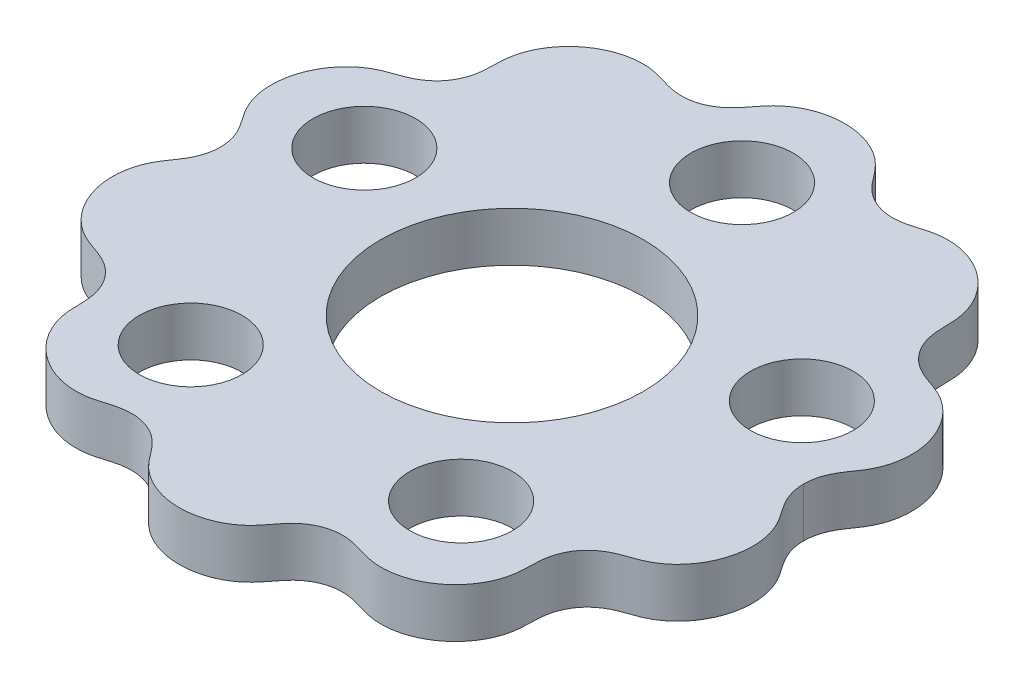
SolidWorks part; units mm, degrees
material "PET"
ref_plane "Front Plane" through (0, 0, 0) normal (0, 0, 1) x (1, 0, 0)
ref_plane "Top Plane" through (0, 0, 0) normal (0, 1, 0) x (1, 0, 0)
ref_plane "Right Plane" through (0, 0, 0) normal (1, 0, 0) x (0, 0, -1)
sketch "Sketch2" plane through (0, 0, 0) normal (0, 1, 0) x (1, 0, 0)
  line L0 (-35.5, 0) -> (35.5, 0) construction
  spline S0 degree 4 poles (33.4858, 18.0026) (33.6819, 17.924) (34.0697, 17.7559) (34.8229, 17.3695) (35.8168, 16.6669) (36.6662, 15.8323) (37.3658, 14.9079) (37.8383, 14.1205) (38.1653, 13.4626) (38.4396, 12.7811) (38.6324, 12.1679) (38.763, 11.6329) (38.856, 11.1412) (38.9196, 10.6952) (38.9638, 10.2049) (38.9806, 9.6712) (38.9658, 9.1373) (38.9248, 8.6719) (38.8693, 8.2752) (38.8096, 7.9474) (38.7602, 7.7184) (38.7131, 7.5241) (38.6709, 7.3649) (38.6347, 7.2368) (38.5942, 7.1034) (38.5498, 6.9652) (38.5069, 6.8376) (38.4719, 6.7392) (38.4232, 6.6091) (38.3681, 6.4683) (38.3132, 6.335) (38.2582, 6.2084) (38.1869, 6.0523) (38.0962, 5.8644) (37.9841, 5.6481) (37.8144, 5.3454) (37.5958, 4.9901) (37.3234, 4.5873) (37.0015, 4.1343) (36.6864, 3.6765) (36.3637, 3.1575) (36.0551, 2.5667) (35.7872, 1.8957) (35.5897, 1.1433) (35.4953, 0.4094) (35.4914, -0.2921) (35.563, -0.9514) (35.6947, -1.5624) (35.9148, -2.2418) (36.2487, -2.9729) (36.7116, -3.7364) (37.2883, -4.5281) (37.8732, -5.3975) (38.3764, -6.3951) (38.8291, -7.7526) (39.0612, -9.4869) (38.9245, -11.2062) (38.4615, -12.8299) (37.8653, -14.1059) (37.2639, -15.0672) (36.5288, -15.9684) (35.6581, -16.7836) (34.7095, -17.4417) (33.7107, -17.9381) (32.726, -18.2865) (31.7989, -18.5913) (30.8389, -19.0081) (29.8914, -19.5994) (29.0166, -20.4069) (28.2897, -21.4373) (27.8234, -22.5309) (27.5826, -23.6177) (27.5037, -24.6512) (27.505, -25.6114) (27.4651, -26.646) (27.3107, -27.5877) (27.0692, -28.4232) (26.6255, -29.5243) (25.9105, -30.7715) (24.7045, -32.1741) (22.8733, -33.4892) (21.0102, -34.2437) (19.2754, -34.5429) (17.8349, -34.5137) (16.7242, -34.3263) (15.7141, -34.0256) (14.7773, -33.7254) (13.7457, -33.4994) (12.6199, -33.4262) (11.4378, -33.5747) (10.2569, -33.9872) (9.2509, -34.5955) (8.4294, -35.3238) (7.7614, -36.1092) (7.196, -36.8901) (6.5586, -37.6989) (5.7796, -38.4701) (4.6502, -39.3075) (3.1026, -40.0593) (1.1762, -40.5363) (-1.0677, -40.5512) (-3.0155, -40.0932) (-4.5978, -39.3403) (-5.7473, -38.4981) (-6.5352, -37.7258) (-7.1782, -36.9144) (-7.7464, -36.1293) (-8.6134, -35.1022) (-9.7345, -34.2099) (-11.1286, -33.6137) (-12.6194, -33.4262) (-13.746, -33.4994) (-14.7771, -33.7254) (-15.7143, -34.0255) (-16.5728, -34.2815) (-17.3671, -34.4346) (-18.2399, -34.5221) (-19.432, -34.5158) (-21.0101, -34.2438) (-22.8733, -33.4892) (-24.7044, -32.1742) (-25.9105, -30.7715) (-26.6256, -29.5243) (-27.0104, -28.5689) (-27.2004, -27.9699) (-27.3615, -27.2769) (-27.4714, -26.489) (-27.5049, -25.6115) (-27.5038, -24.6512) (-27.5826, -23.6178) (-27.8234, -22.5309) (-28.2897, -21.4374) (-29.0166, -20.4069) (-29.8914, -19.5994) (-30.8389, -19.0081) (-31.7989, -18.5913) (-32.726, -18.2865) (-33.7107, -17.9381) (-34.7095, -17.4417) (-35.6581, -16.7836) (-36.5288, -15.9684) (-37.2639, -15.0672) (-37.8653, -14.1059) (-38.4615, -12.8299) (-38.9245, -11.2062) (-39.0612, -9.4869) (-38.8291, -7.7526) (-38.3764, -6.3951) (-37.8732, -5.3975) (-37.2883, -4.5281) (-36.7116, -3.7364) (-36.2487, -2.9729) (-35.9148, -2.2418) (-35.6947, -1.5624) (-35.563, -0.9514) (-35.4914, -0.2921) (-35.4953, 0.4094) (-35.5897, 1.1433) (-35.7872, 1.8957) (-36.0551, 2.5667) (-36.3637, 3.1575) (-36.6864, 3.6765) (-37.0015, 4.1343) (-37.3234, 4.5873) (-37.5958, 4.9901) (-37.8144, 5.3454) (-37.9841, 5.6481) (-38.0962, 5.8644) (-38.1869, 6.0523) (-38.2582, 6.2084) (-38.3132, 6.335) (-38.3681, 6.4683) (-38.4232, 6.6091) (-38.4719, 6.7392) (-38.5069, 6.8376) (-38.5498, 6.9652) (-38.5942, 7.1034) (-38.6347, 7.2368) (-38.6709, 7.3649) (-38.7131, 7.5241) (-38.7602, 7.7184) (-38.8096, 7.9474) (-38.8693, 8.2752) (-38.9248, 8.6719) (-38.9658, 9.1373) (-38.9806, 9.6712) (-38.9638, 10.2049) (-38.9114, 10.7866) (-38.8136, 11.4133) (-38.6599, 12.0804) (-38.4396, 12.7811) (-38.1653, 13.4626) (-37.8383, 14.1205) (-37.3658, 14.9079) (-36.6662, 15.8323) (-35.8168, 16.6669) (-34.8229, 17.3695) (-34.0697, 17.7559) (-33.6819, 17.924) (-33.4858, 18.0026) knots 0 0 0 0 0 0.004809 0.009619 0.019238 0.027591 0.031768 0.035945 0.040122 0.044299 0.048476 0.050565 0.052653 0.055691 0.058728 0.061766 0.064804 0.067841 0.06936 0.070879 0.072398 0.073157 0.073916 0.074676 0.075435 0.076195 0.076954 0.077745 0.078536 0.079326 0.080117 0.080908 0.081698 0.08328 0.084861 0.086443 0.089606 0.092769 0.095932 0.099095 0.102258 0.106673 0.111089 0.115505 0.11992 0.123472 0.127023 0.130575 0.134126 0.139703 0.145279 0.150856 0.156432 0.163531 0.17063 0.183308 0.195985 0.202422 0.20886 0.215297 0.221734 0.22883 0.235926 0.241481 0.247037 0.252592 0.258148 0.265247 0.272347 0.279497 0.286646 0.292113 0.297579 0.303046 0.308512 0.315658 0.31923 0.322803 0.335512 0.348221 0.360938 0.373655 0.380833 0.388011 0.39361 0.39921 0.404809 0.410408 0.417591 0.424773 0.431727 0.438681 0.44417 0.44966 0.455149 0.460639 0.467587 0.474534 0.487038 0.499543 0.512347 0.52515 0.532151 0.539153 0.544668 0.550183 0.555698 0.561213 0.575227 0.582409 0.589592 0.595191 0.60079 0.60639 0.611989 0.615578 0.619167 0.626345 0.639062 0.651779 0.664488 0.677197 0.68077 0.684342 0.687915 0.691488 0.696954 0.702421 0.707887 0.713354 0.720503 0.727653 0.734753 0.741852 0.747408 0.752963 0.758519 0.764074 0.77117 0.778266 0.784703 0.79114 0.797578 0.804015 0.816692 0.82937 0.836469 0.843568 0.849144 0.854721 0.860297 0.865874 0.869425 0.872977 0.876528 0.88008 0.884495 0.888911 0.893327 0.897742 0.900905 0.904068 0.907231 0.910394 0.913557 0.915139 0.91672 0.918302 0.919092 0.919883 0.920674 0.921464 0.922255 0.923046 0.923805 0.924565 0.925324 0.926084 0.926843 0.927602 0.929121 0.93064 0.932159 0.935196 0.938234 0.941272 0.944309 0.947347 0.951524 0.955701 0.959878 0.964055 0.968232 0.972409 0.980762 0.990381 0.995191 1 1 1 1 1 construction
  spline S1 degree 4 poles (35.5, 0) (35.5, -0.0043) (35.5002, -0.1647) (35.5119, -0.481) (35.563, -0.9514) (35.6947, -1.5624) (35.9148, -2.2418) (36.2487, -2.9729) (36.7116, -3.7364) (37.2883, -4.5281) (37.8732, -5.3975) (38.3764, -6.3951) (38.8291, -7.7526) (39.0612, -9.4869) (38.9245, -11.2062) (38.4615, -12.8299) (37.8653, -14.1059) (37.2639, -15.0672) (36.5288, -15.9684) (35.6581, -16.7836) (34.7095, -17.4417) (33.7107, -17.9381) (32.726, -18.2865) (31.7989, -18.5913) (30.8389, -19.0081) (29.8914, -19.5994) (29.0166, -20.4069) (28.2897, -21.4373) (27.8234, -22.5309) (27.5826, -23.6177) (27.5037, -24.6512) (27.505, -25.6114) (27.4651, -26.646) (27.3107, -27.5877) (27.0692, -28.4232) (26.6255, -29.5243) (25.9105, -30.7715) (24.7045, -32.1741) (22.8733, -33.4892) (21.0102, -34.2437) (19.2754, -34.5429) (17.8349, -34.5137) (16.7242, -34.3263) (15.7141, -34.0256) (14.7773, -33.7254) (13.7457, -33.4994) (12.6199, -33.4262) (11.4378, -33.5747) (10.2569, -33.9872) (9.2509, -34.5955) (8.4294, -35.3238) (7.7614, -36.1092) (7.196, -36.8901) (6.5586, -37.6989) (5.7796, -38.4701) (4.6502, -39.3075) (3.1026, -40.0593) (1.1762, -40.5363) (-1.0677, -40.5512) (-3.0155, -40.0932) (-4.5978, -39.3403) (-5.7473, -38.4981) (-6.5352, -37.7258) (-7.1782, -36.9144) (-7.7464, -36.1293) (-8.6134, -35.1022) (-9.7345, -34.2099) (-11.1286, -33.6137) (-12.6194, -33.4262) (-13.746, -33.4994) (-14.7771, -33.7254) (-15.7143, -34.0255) (-16.5728, -34.2815) (-17.3671, -34.4346) (-18.2399, -34.5221) (-19.432, -34.5158) (-21.0101, -34.2438) (-22.8733, -33.4892) (-24.7044, -32.1742) (-25.9105, -30.7715) (-26.6256, -29.5243) (-27.0104, -28.5689) (-27.2004, -27.9699) (-27.3615, -27.2769) (-27.4714, -26.489) (-27.5049, -25.6115) (-27.5038, -24.6512) (-27.5826, -23.6178) (-27.8234, -22.5309) (-28.2897, -21.4374) (-29.0166, -20.4069) (-29.8914, -19.5994) (-30.8389, -19.0081) (-31.7989, -18.5913) (-32.726, -18.2865) (-33.7107, -17.9381) (-34.7095, -17.4417) (-35.6581, -16.7836) (-36.5288, -15.9684) (-37.2639, -15.0672) (-37.8653, -14.1059) (-38.4615, -12.8299) (-38.9245, -11.2062) (-39.0612, -9.4869) (-38.8291, -7.7526) (-38.3764, -6.3951) (-37.8732, -5.3975) (-37.2883, -4.5281) (-36.7116, -3.7364) (-36.2487, -2.9729) (-35.9148, -2.2418) (-35.6947, -1.5624) (-35.563, -0.9514) (-35.5119, -0.481) (-35.5002, -0.1647) (-35.5, -0.0043) (-35.5, 0) knots 0.119822 0.119822 0.119822 0.119822 0.119822 0.11992 0.123472 0.127023 0.130575 0.134126 0.139703 0.145279 0.150856 0.156432 0.163531 0.17063 0.183308 0.195985 0.202422 0.20886 0.215297 0.221734 0.22883 0.235926 0.241481 0.247037 0.252592 0.258148 0.265247 0.272347 0.279497 0.286646 0.292113 0.297579 0.303046 0.308512 0.315658 0.31923 0.322803 0.335512 0.348221 0.360938 0.373655 0.380833 0.388011 0.39361 0.39921 0.404809 0.410408 0.417591 0.424773 0.431727 0.438681 0.44417 0.44966 0.455149 0.460639 0.467587 0.474534 0.487038 0.499543 0.512347 0.52515 0.532151 0.539153 0.544668 0.550183 0.555698 0.561213 0.575227 0.582409 0.589592 0.595191 0.60079 0.60639 0.611989 0.615578 0.619167 0.626345 0.639062 0.651779 0.664488 0.677197 0.68077 0.684342 0.687915 0.691488 0.696954 0.702421 0.707887 0.713354 0.720503 0.727653 0.734753 0.741852 0.747408 0.752963 0.758519 0.764074 0.77117 0.778266 0.784703 0.79114 0.797578 0.804015 0.816692 0.82937 0.836469 0.843568 0.849144 0.854721 0.860297 0.865874 0.869425 0.872977 0.876528 0.88008 0.880178 0.880178 0.880178 0.880178 0.880178
  spline S2 degree 4 poles (35.5, 0) (35.5, 0.0043) (35.5002, 0.1647) (35.5119, 0.481) (35.563, 0.9514) (35.6947, 1.5624) (35.9148, 2.2418) (36.2487, 2.9729) (36.7116, 3.7364) (37.2883, 4.5281) (37.8732, 5.3975) (38.3764, 6.3951) (38.8291, 7.7526) (39.0612, 9.4869) (38.9245, 11.2062) (38.4615, 12.8299) (37.8653, 14.1059) (37.2639, 15.0672) (36.5288, 15.9684) (35.6581, 16.7836) (34.7095, 17.4417) (33.7107, 17.9381) (32.726, 18.2865) (31.7989, 18.5913) (30.8389, 19.0081) (29.8914, 19.5994) (29.0166, 20.4069) (28.2897, 21.4373) (27.8234, 22.5309) (27.5826, 23.6177) (27.5037, 24.6512) (27.505, 25.6114) (27.4651, 26.646) (27.3107, 27.5877) (27.0692, 28.4232) (26.6255, 29.5243) (25.9105, 30.7715) (24.7045, 32.1741) (22.8733, 33.4892) (21.0102, 34.2437) (19.2754, 34.5429) (17.8349, 34.5137) (16.7242, 34.3263) (15.7141, 34.0256) (14.7773, 33.7254) (13.7457, 33.4994) (12.6199, 33.4262) (11.4378, 33.5747) (10.2569, 33.9872) (9.2509, 34.5955) (8.4294, 35.3238) (7.7614, 36.1092) (7.196, 36.8901) (6.5586, 37.6989) (5.7796, 38.4701) (4.6502, 39.3075) (3.1026, 40.0593) (1.1762, 40.5363) (-1.0677, 40.5512) (-3.0155, 40.0932) (-4.5978, 39.3403) (-5.7473, 38.4981) (-6.5352, 37.7258) (-7.1782, 36.9144) (-7.7464, 36.1293) (-8.6134, 35.1022) (-9.7345, 34.2099) (-11.1286, 33.6137) (-12.6194, 33.4262) (-13.746, 33.4994) (-14.7771, 33.7254) (-15.7143, 34.0255) (-16.5728, 34.2815) (-17.3671, 34.4346) (-18.2399, 34.5221) (-19.432, 34.5158) (-21.0101, 34.2438) (-22.8733, 33.4892) (-24.7044, 32.1742) (-25.9105, 30.7715) (-26.6256, 29.5243) (-27.0104, 28.5689) (-27.2004, 27.9699) (-27.3615, 27.2769) (-27.4714, 26.489) (-27.5049, 25.6115) (-27.5038, 24.6512) (-27.5826, 23.6178) (-27.8234, 22.5309) (-28.2897, 21.4374) (-29.0166, 20.4069) (-29.8914, 19.5994) (-30.8389, 19.0081) (-31.7989, 18.5913) (-32.726, 18.2865) (-33.7107, 17.9381) (-34.7095, 17.4417) (-35.6581, 16.7836) (-36.5288, 15.9684) (-37.2639, 15.0672) (-37.8653, 14.1059) (-38.4615, 12.8299) (-38.9245, 11.2062) (-39.0612, 9.4869) (-38.8291, 7.7526) (-38.3764, 6.3951) (-37.8732, 5.3975) (-37.2883, 4.5281) (-36.7116, 3.7364) (-36.2487, 2.9729) (-35.9148, 2.2418) (-35.6947, 1.5624) (-35.563, 0.9514) (-35.5119, 0.481) (-35.5002, 0.1647) (-35.5, 0.0043) (-35.5, 0) knots 0.119822 0.119822 0.119822 0.119822 0.119822 0.11992 0.123472 0.127023 0.130575 0.134126 0.139703 0.145279 0.150856 0.156432 0.163531 0.17063 0.183308 0.195985 0.202422 0.20886 0.215297 0.221734 0.22883 0.235926 0.241481 0.247037 0.252592 0.258148 0.265247 0.272347 0.279497 0.286646 0.292113 0.297579 0.303046 0.308512 0.315658 0.31923 0.322803 0.335512 0.348221 0.360938 0.373655 0.380833 0.388011 0.39361 0.39921 0.404809 0.410408 0.417591 0.424773 0.431727 0.438681 0.44417 0.44966 0.455149 0.460639 0.467587 0.474534 0.487038 0.499543 0.512347 0.52515 0.532151 0.539153 0.544668 0.550183 0.555698 0.561213 0.575227 0.582409 0.589592 0.595191 0.60079 0.60639 0.611989 0.615578 0.619167 0.626345 0.639062 0.651779 0.664488 0.677197 0.68077 0.684342 0.687915 0.691488 0.696954 0.702421 0.707887 0.713354 0.720503 0.727653 0.734753 0.741852 0.747408 0.752963 0.758519 0.764074 0.77117 0.778266 0.784703 0.79114 0.797578 0.804015 0.816692 0.82937 0.836469 0.843568 0.849144 0.854721 0.860297 0.865874 0.869425 0.872977 0.876528 0.88008 0.880178 0.880178 0.880178 0.880178 0.880178
extrude "Boss-Extrude1" add sketch "Sketch2" along normal blind 6
sketch "Sketch3" plane through (0, 6, 0) normal (0, 1, 0) x (1, 0, 0)
  line L0 (0, 0) -> (35.5, 0) construction
  line L1 (0, 0) -> (38.5178, 12.5153) construction
  circle A0 centre (0, 0) radius 16
  circle A1 centre (26.6296, 8.6525) radius 6.25
  circle A2 centre (16.458, -22.6524) radius 6.25
  circle A3 centre (-16.4579, -22.6525) radius 6.25
  circle A4 centre (-26.6296, 8.6524) radius 6.25
  circle A5 centre (0, 28) radius 6.25
  spline S0 degree 4 poles (35.5, 0) (35.5, 0.0043) (35.5002, 0.1647) (35.5119, 0.481) (35.563, 0.9514) (35.6947, 1.5624) (35.9148, 2.2418) (36.2487, 2.9729) (36.7116, 3.7364) (37.2883, 4.5281) (37.8732, 5.3975) (38.3764, 6.3951) (38.8291, 7.7526) (39.0612, 9.4869) (38.9245, 11.2062) (38.4615, 12.8299) (37.8653, 14.1059) (37.2639, 15.0672) (36.5288, 15.9684) (35.6581, 16.7836) (34.7095, 17.4417) (33.7107, 17.9381) (32.726, 18.2865) (31.7989, 18.5913) (30.8389, 19.0081) (29.8914, 19.5994) (29.0166, 20.4069) (28.2897, 21.4373) (27.8234, 22.5309) (27.5826, 23.6177) (27.5037, 24.6512) (27.505, 25.6114) (27.4651, 26.646) (27.3107, 27.5877) (27.0692, 28.4232) (26.6255, 29.5243) (25.9105, 30.7715) (24.7045, 32.1741) (22.8733, 33.4892) (21.0102, 34.2437) (19.2754, 34.5429) (17.8349, 34.5137) (16.7242, 34.3263) (15.7141, 34.0256) (14.7773, 33.7254) (13.7457, 33.4994) (12.6199, 33.4262) (11.4378, 33.5747) (10.2569, 33.9872) (9.2509, 34.5955) (8.4294, 35.3238) (7.7614, 36.1092) (7.196, 36.8901) (6.5586, 37.6989) (5.7796, 38.4701) (4.6502, 39.3075) (3.1026, 40.0593) (1.1762, 40.5363) (-1.0677, 40.5512) (-3.0155, 40.0932) (-4.5978, 39.3403) (-5.7473, 38.4981) (-6.5352, 37.7258) (-7.1782, 36.9144) (-7.7464, 36.1293) (-8.6134, 35.1022) (-9.7345, 34.2099) (-11.1286, 33.6137) (-12.6194, 33.4262) (-13.746, 33.4994) (-14.7771, 33.7254) (-15.7143, 34.0255) (-16.5728, 34.2815) (-17.3671, 34.4346) (-18.2399, 34.5221) (-19.432, 34.5158) (-21.0101, 34.2438) (-22.8733, 33.4892) (-24.7044, 32.1742) (-25.9105, 30.7715) (-26.6256, 29.5243) (-27.0104, 28.5689) (-27.2004, 27.9699) (-27.3615, 27.2769) (-27.4714, 26.489) (-27.5049, 25.6115) (-27.5038, 24.6512) (-27.5826, 23.6178) (-27.8234, 22.5309) (-28.2897, 21.4374) (-29.0166, 20.4069) (-29.8914, 19.5994) (-30.8389, 19.0081) (-31.7989, 18.5913) (-32.726, 18.2865) (-33.7107, 17.9381) (-34.7095, 17.4417) (-35.6581, 16.7836) (-36.5288, 15.9684) (-37.2639, 15.0672) (-37.8653, 14.1059) (-38.4615, 12.8299) (-38.9245, 11.2062) (-39.0612, 9.4869) (-38.8291, 7.7526) (-38.3764, 6.3951) (-37.8732, 5.3975) (-37.2883, 4.5281) (-36.7116, 3.7364) (-36.2487, 2.9729) (-35.9148, 2.2418) (-35.6947, 1.5624) (-35.563, 0.9514) (-35.5119, 0.481) (-35.5002, 0.1647) (-35.5, 0.0043) (-35.5, 0) knots 0.119822 0.119822 0.119822 0.119822 0.119822 0.11992 0.123472 0.127023 0.130575 0.134126 0.139703 0.145279 0.150856 0.156432 0.163531 0.17063 0.183308 0.195985 0.202422 0.20886 0.215297 0.221734 0.22883 0.235926 0.241481 0.247037 0.252592 0.258148 0.265247 0.272347 0.279497 0.286646 0.292113 0.297579 0.303046 0.308512 0.315658 0.31923 0.322803 0.335512 0.348221 0.360938 0.373655 0.380833 0.388011 0.39361 0.39921 0.404809 0.410408 0.417591 0.424773 0.431727 0.438681 0.44417 0.44966 0.455149 0.460639 0.467587 0.474534 0.487038 0.499543 0.512347 0.52515 0.532151 0.539153 0.544668 0.550183 0.555698 0.561213 0.575227 0.582409 0.589592 0.595191 0.60079 0.60639 0.611989 0.615578 0.619167 0.626345 0.639062 0.651779 0.664488 0.677197 0.68077 0.684342 0.687915 0.691488 0.696954 0.702421 0.707887 0.713354 0.720503 0.727653 0.734753 0.741852 0.747408 0.752963 0.758519 0.764074 0.77117 0.778266 0.784703 0.79114 0.797578 0.804015 0.816692 0.82937 0.836469 0.843568 0.849144 0.854721 0.860297 0.865874 0.869425 0.872977 0.876528 0.88008 0.880178 0.880178 0.880178 0.880178 0.880178 construction
  point P21 (0, 0)
  dimension "D1" = 32
  dimension "D2" = 12.5
  dimension "D3" = 28
extrude "Cut-Extrude1" cut sketch "Sketch3" against normal blind 6
